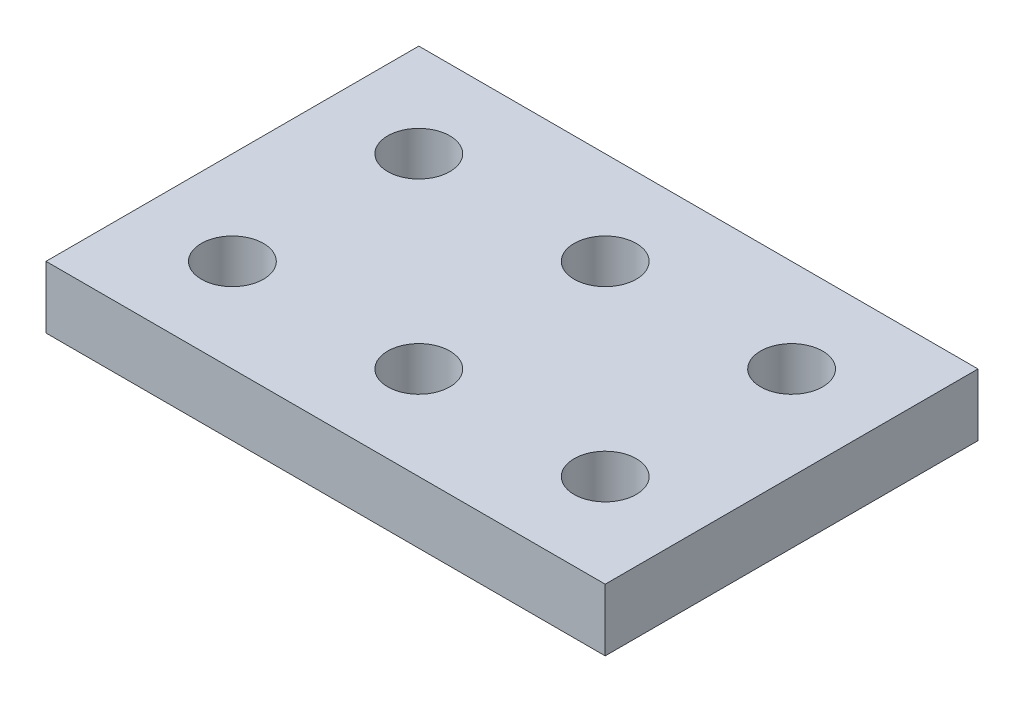
SolidWorks part; units mm, degrees
ref_plane "Front Plane" through (0, 0, 0) normal (0, 0, 1) x (1, 0, 0)
ref_plane "Top Plane" through (0, 0, 0) normal (0, 1, 0) x (1, 0, 0)
ref_plane "Right Plane" through (0, 0, 0) normal (1, 0, 0) x (0, 0, -1)
sketch "Sketch1" plane through (0, 0, 0) normal (0, 1, 0) x (1, 0, 0)
  line L0 (0, 0) -> (90, 0)
  line L1 (90, 0) -> (90, 60)
  line L2 (90, 60) -> (0, 60)
  line L3 (0, 60) -> (0, 0)
  circle A0 centre (15, 45) radius 5
  circle A1 centre (45, 45) radius 5
  circle A2 centre (75, 45) radius 5
  circle A3 centre (45, 15) radius 5
  circle A4 centre (75, 15) radius 5
  circle A5 centre (15, 15) radius 5
  dimension "D4" = 15
  dimension "D5" = 10
  dimension "D1" = 90
  dimension "D2" = 60
  dimension "D3" = 15
  dimension "D6" = 3
  dimension "D7" = 2
extrude "Boss-Extrude1" add sketch "Sketch1" along normal blind 10
